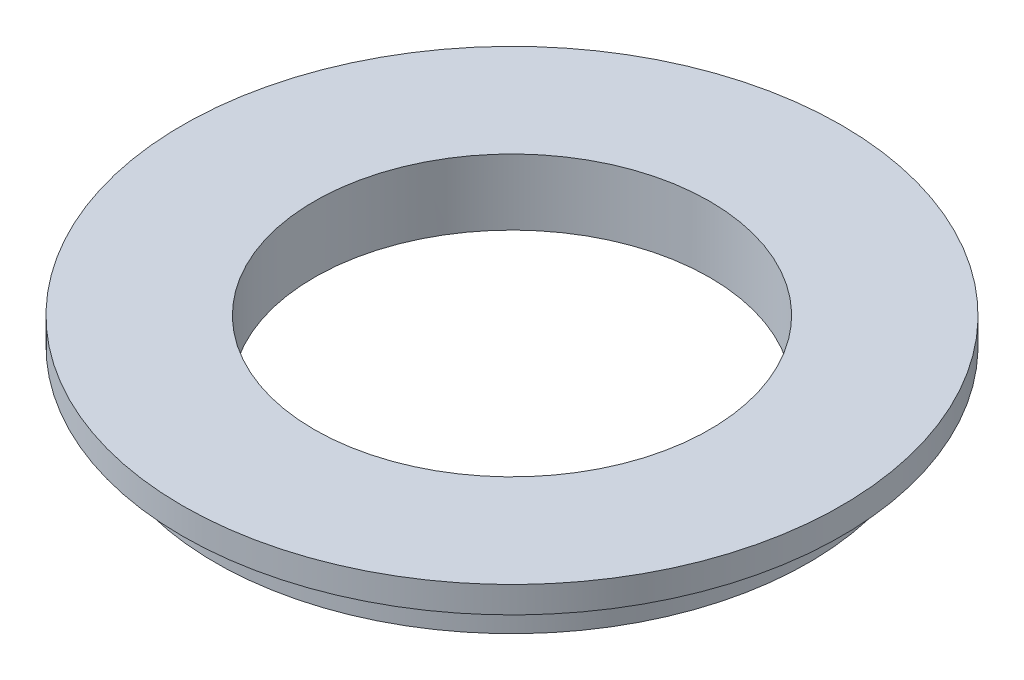
SolidWorks part; units mm, degrees
ref_plane "Front Plane" through (0, 0, 0) normal (0, 0, 1) x (1, 0, 0)
ref_plane "Top Plane" through (0, 0, 0) normal (0, 1, 0) x (1, 0, 0)
ref_plane "Right Plane" through (0, 0, 0) normal (1, 0, 0) x (0, 0, -1)
sketch "Sketch1" plane through (0, 0, 0) normal (0, 1, 0) x (1, 0, 0)
  circle A0 centre (0, 0) radius 25
  circle A1 centre (0, 0) radius 15
  dimension "D1" = 50
  dimension "D2" = 30
extrude "Boss-Extrude1" add sketch "Sketch1" along normal blind 2
sketch "Sketch2" plane through (0, 0, 0) normal (0, -1, 0) x (1, 0, 0)
  circle A0 centre (0, 0) radius 22.5
  circle A1 centre (0, 0) radius 15 construction
  circle A2 centre (0, 0) radius 15
  dimension "D1" = 45
extrude "Boss-Extrude2" add sketch "Sketch2" along normal blind 3
